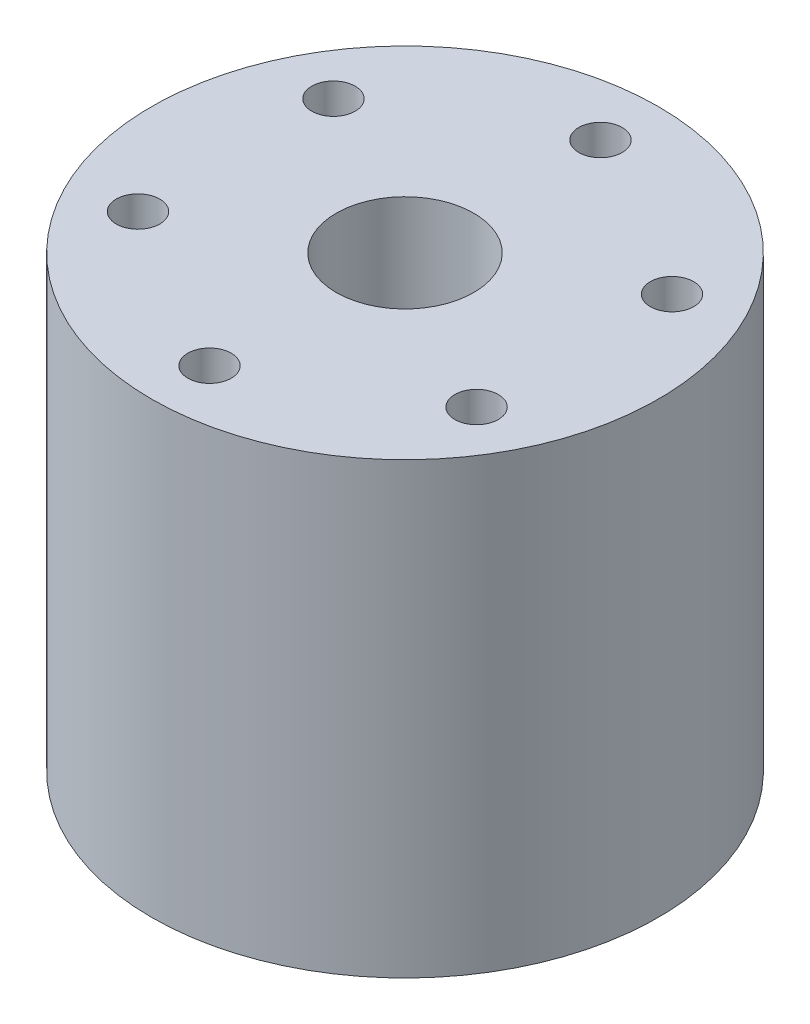
SolidWorks part; units mm, degrees
ref_plane "前视基准面" through (0, 0, 0) normal (0, 0, 1) x (1, 0, 0)
ref_plane "上视基准面" through (0, 0, 0) normal (0, 1, 0) x (1, 0, 0)
ref_plane "右视基准面" through (0, 0, 0) normal (1, 0, 0) x (0, 0, -1)
sketch "草图1" plane through (0, 0, 0) normal (0, 1, 0) x (1, 0, 0)
  line L0 (0, 34.1091) -> (0, -33.6188) construction
  circle A0 centre (0, 0) radius 17.5
  circle A1 centre (0, 0) radius 13.5 construction
  circle A2 centre (11.6913, 6.75) radius 1.5
  circle A3 centre (0, 0) radius 4.75
  circle A4 centre (0, 13.5) radius 1.5
  circle A5 centre (11.6913, -6.75) radius 1.5
  circle A6 centre (0, -13.5) radius 1.5
  circle A7 centre (-11.6913, -6.75) radius 1.5
  circle A8 centre (-11.6913, 6.75) radius 1.5
  point P14 (0, 0)
  point P23 (0, 0)
  point P25 (0, 0)
  dimension "D1" = 35
  dimension "D2" = 27
  dimension "D3" = 6
  dimension "D4" = 9.5
  dimension "D8" = 3
extrude "凸台-拉伸1" add sketch "草图1" along normal blind 31
